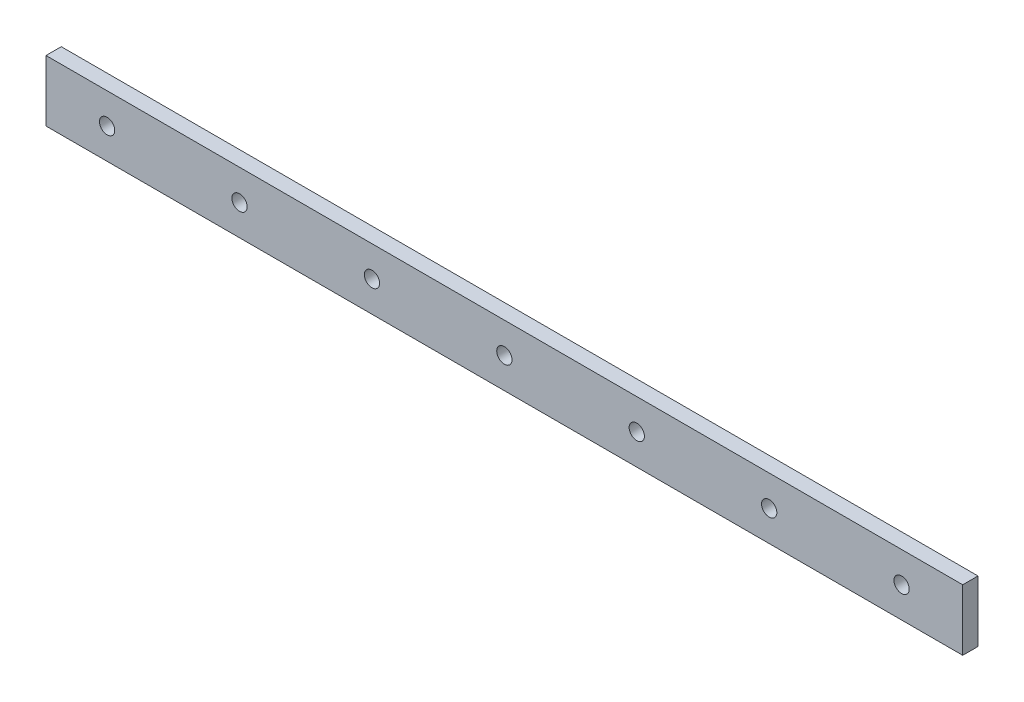
SolidWorks part; units mm, degrees
ref_plane "Přední rovina" through (0, 0, 0) normal (0, 0, 1) x (1, 0, 0)
ref_plane "Horní rovina" through (0, 0, 0) normal (0, 1, 0) x (1, 0, 0)
ref_plane "Pravá rovina" through (0, 0, 0) normal (1, 0, 0) x (0, 0, -1)
sketch "Skica1" plane through (0, 0, 0) normal (0, 0, 1) x (1, 0, 0)
  line L1 (-150, 10) -> (150, 10)
  line L2 (-150, 10) -> (-150, -10)
  line L3 (-150, -10) -> (150, -10)
  line L4 (150, 10) -> (150, -10)
  line L5 (-150, 10) -> (150, -10) construction
  line L6 (-150, -10) -> (150, 10) construction
  point P0 (0, 0)
  dimension "D1" = 300
  dimension "D2" = 20
extrude "Přidat vysunutím1" add sketch "Skica1" along normal blind 5
hole_wizard "Ø5.0 (5) průměr díry1" positions "Skica3" profile "Skica2" hole size "Ø5.0" standard "ANSI Metric" end condition through all
sketch "Skica3" plane through (0, 0, 5) normal (0, 0, 1) x (1, 0, 0)
  line L0 (-150, 10) -> (-150, -10) construction
  point P0 (-130, 0)
  dimension "D1" = 20
sketch "Skica2" plane through (-130, 0, 5) normal (1, 0, 0) x (0, -1, 0)
  line L0 (0, 0) -> (0, 5)
  line L1 (0, 5) -> (2.5, 5)
  line L2 (2.5, 5) -> (2.5, 0)
  line L5 (2.5, 0) -> (0, 0)
  line L11 (0, -6.35) -> (0, 107.95) construction
  dimension "Průměr díry skrz" = 5
  dimension "Hloubka díry skrz" = 5
hole_wizard "Ø5.0 (5) průměr díry2" positions "Skica5" profile "Skica4" hole size "Ø5.0" standard "ANSI Metric" end condition through all
sketch "Skica5" plane through (0, 0, 5) normal (0, 0, 1) x (1, 0, 0)
  line L0 (150, -10) -> (150, 10) construction
  point P0 (130, 0)
  dimension "D1" = 20
sketch "Skica4" plane through (130, 0, 5) normal (1, 0, 0) x (0, -1, 0)
  line L0 (0, 0) -> (0, 5)
  line L1 (0, 5) -> (2.5, 5)
  line L2 (2.5, 5) -> (2.5, 0)
  line L5 (2.5, 0) -> (0, 0)
  line L11 (0, -6.35) -> (0, 107.95) construction
  dimension "Průměr díry skrz" = 5
  dimension "Hloubka díry skrz" = 5
pattern_linear "LinPole1" count 6 spacing 43.3333 along (1, 0, 0) of "Ø5.0 (5) průměr díry1"
equation "\"roztec\"= ( \"D1@Skica1\" - \"D1@Skica3\" - \"D1@Skica5\" ) / \"D1@LinPole1\""
equation "\"D3@LinPole1\"= \"roztec\""
